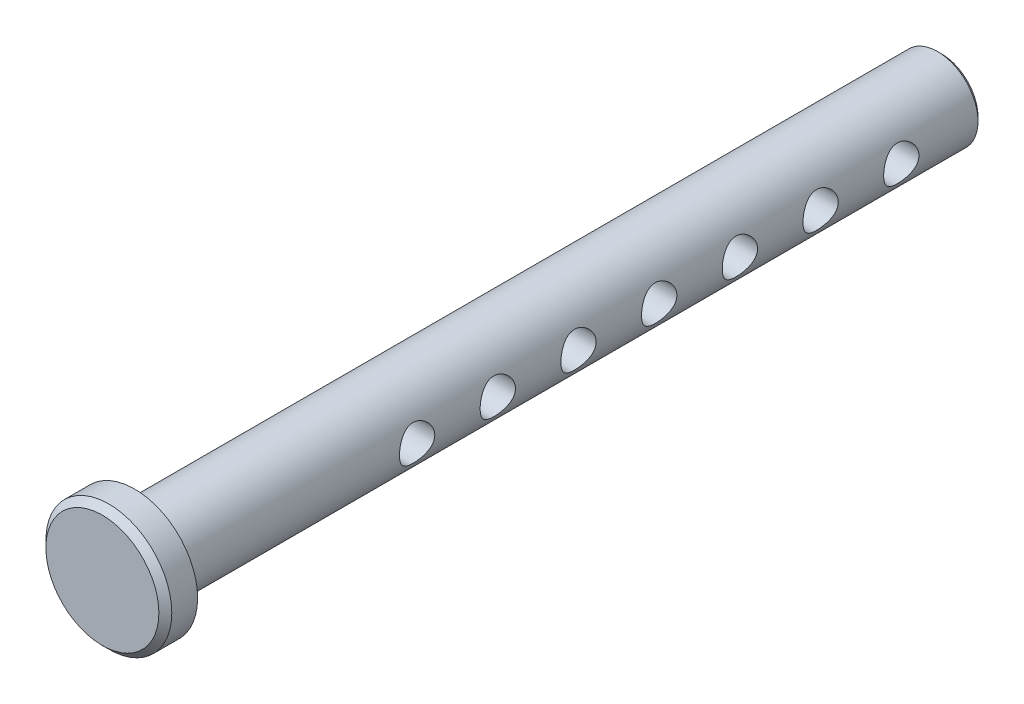
SolidWorks part; units mm, degrees
ref_plane "Front" through (0, 0, 0) normal (0, 0, 1) x (1, 0, 0)
ref_plane "Top" through (0, 0, 0) normal (0, 1, 0) x (1, 0, 0)
ref_plane "Right" through (0, 0, 0) normal (1, 0, 0) x (0, 0, -1)
sketch "Sketch1" plane through (0, 0, 0) normal (0, 0, 1) x (1, 0, 0)
  circle A0 centre (0, 0) radius 3.175
  point P3 (0, 3.175)
  point P4 (0, -3.175)
  dimension "dia" = 6.35
extrude "Extrude1" add sketch "Sketch1" along normal mid plane 63.5
sketch "Sketch2" plane through (0, 0, 31.75) normal (0, 0, 1) x (1, 0, 0)
  circle A0 centre (0, 0) radius 4.953
  dimension "head dia" = 9.906
extrude "Extrude2" add sketch "Sketch2" along normal blind 2.54
chamfer "Chamfer1" distance 0.508 angle 45 1 edges at (4.953, 0, 34.29)
sketch "Sketch3" plane through (0, 0, 0) normal (1, 0, 0) x (0, 0, -1)
  line L1 (31.75, -3.175) -> (31.75, 3.175) construction
  circle A0 centre (25.4, 0) radius 1.3891
  point P2 (24.0109, 0)
  dimension "D1" = 6.35
  dimension "hole dia" = 2.7781
extrude "Extrude3" cut sketch "Sketch3" against normal through all and the other way through all
pattern_linear "LPattern1" count 7 spacing 6.35 along (0, 0, 1) of "Extrude3"
chamfer "Chamfer2" distance 0.3175 angle 45 1 edges at (3.175, 0, -31.75)
ref_plane "Plane1" through (0, 0, -25.4) normal (0, 0, 1) x (1, 0, 0)
sketch "Sketch8" plane through (0, 0, 0) normal (1, 0, 0) x (0, 0, -1)
  line L0 (-34.29, 4.445) -> (-34.29, -4.445) construction
  line L1 (-33.782, -4.953) -> (-31.75, -4.953) construction
  line L2 (31.75, -2.8575) -> (31.75, 2.8575) construction
  circle A0 centre (19.05, 0) radius 1.3891 construction
  circle A1 centre (25.4, 0) radius 1.3891 construction
  point P0 (-34.29, 4.953)
  point P1 (-31.75, 4.953)
  point P5 (31.75, 3.175)
  point P8 (-34.29, -4.953)
  point P9 (31.75, -3.175)
  point P12 (25.4, 0)
  point P13 (19.05, 0)
  point P17 (19.05, -1.3891)
  point P19 (25.4, -1.3891)
equation "\"D1@Chamfer1\" = \"head ht@Extrude2\" * .2"
equation "\"D1@Chamfer2\" = \"dia@Sketch1\" * .05"
